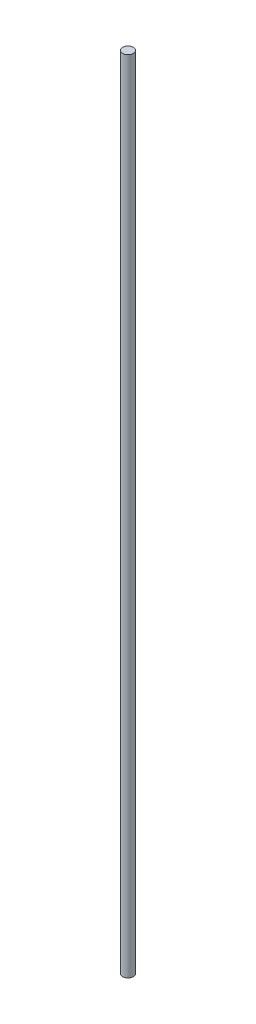
SolidWorks part; units mm, degrees
ref_plane "Front" through (0, 0, 0) normal (0, 0, 1) x (1, 0, 0)
ref_plane "Top" through (0, 0, 0) normal (0, 1, 0) x (1, 0, 0)
ref_plane "Right" through (0, 0, 0) normal (1, 0, 0) x (0, 0, -1)
sketch "Sketch1" plane through (0, 0, 0) normal (0, 1, 0) x (1, 0, 0)
  circle A0 centre (0, 0) radius 10
  dimension "D1" = 20
extrude "Boss-Extrude1" add sketch "Sketch1" along normal blind 1500
